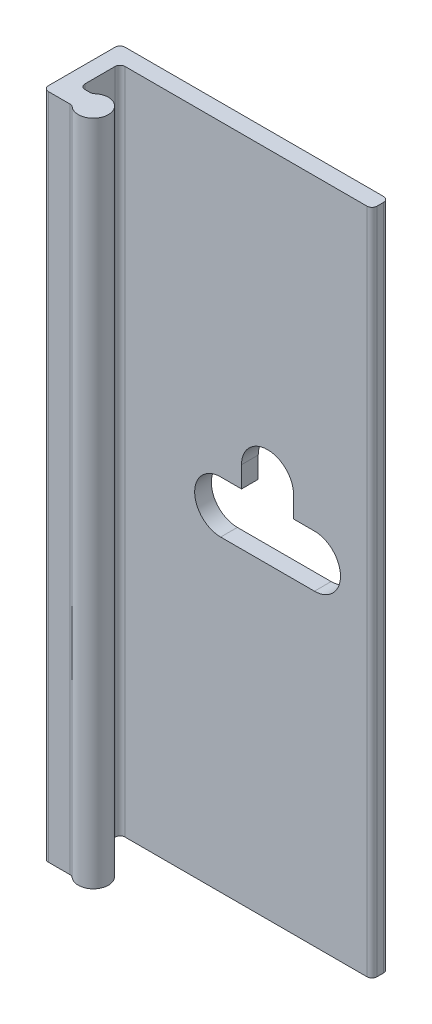
SolidWorks part; units mm, degrees
ref_plane "Front Plane" through (0, 0, 0) normal (0, 0, 1) x (1, 0, 0)
ref_plane "Top Plane" through (0, 0, 0) normal (0, 1, 0) x (1, 0, 0)
ref_plane "Right Plane" through (0, 0, 0) normal (1, 0, 0) x (0, 0, -1)
sketch "Sketch2" plane through (0, 0, 0) normal (0, 1, 0) x (1, 0, 0)
  line L0 (0, 7.209) -> (0, -15.6826) construction
  line L16 (-5.969, 0) -> (19.431, 0)
  line L18 (19.812, -0.381) -> (19.812, -0.889)
  line L19 (19.431, -1.27) -> (1.016, -1.27)
  line L20 (0.635, -1.651) -> (0.635, -3.937)
  line L52 (-0.635, -1.651) -> (-0.635, -3.937)
  line L53 (-8.0148, -5.08) -> (8.0148, -5.08) construction
  line L54 (-1.405, -4.318) -> (-1.016, -4.318)
  line L55 (-1.405, -5.842) -> (1.405, -5.842)
  line L56 (1.016, -4.318) -> (1.405, -4.318)
  line L57 (-1.016, -1.27) -> (-5.969, -1.27)
  line L58 (-6.35, -0.889) -> (-6.35, -0.381)
  arc A11 (19.431, 0) -> (19.812, -0.381) centre (19.431, -0.381) cw
  arc A12 (19.812, -0.889) -> (19.431, -1.27) centre (19.431, -0.889) cw
  arc A19 (1.016, -1.27) -> (0.635, -1.651) centre (1.016, -1.651) ccw
  arc A20 (-1.657, -4.2227) -> (-1.657, -5.9373) centre (-2.413, -5.08) ccw
  arc A21 (1.657, -5.9373) -> (1.657, -4.2227) centre (2.413, -5.08) ccw
  arc A22 (0.635, -3.937) -> (1.016, -4.318) centre (1.016, -3.937) ccw
  arc A23 (-0.635, -3.937) -> (-1.016, -4.318) centre (-1.016, -3.937) cw
  arc A24 (1.405, -5.842) -> (1.657, -5.9373) centre (1.405, -6.223) cw
  arc A25 (1.657, -4.2227) -> (1.405, -4.318) centre (1.405, -3.937) cw
  arc A26 (-1.405, -5.842) -> (-1.657, -5.9373) centre (-1.405, -6.223) ccw
  arc A27 (-1.405, -4.318) -> (-1.657, -4.2227) centre (-1.405, -3.937) cw
  arc A28 (-6.35, -0.381) -> (-5.969, 0) centre (-5.969, -0.381) cw
  arc A29 (-5.969, -1.27) -> (-6.35, -0.889) centre (-5.969, -0.889) cw
  arc A30 (-1.016, -1.27) -> (-0.635, -1.651) centre (-1.016, -1.651) cw
  point P7 (0, -5.08)
  point P16 (19.812, 0)
  point P19 (19.812, -1.27)
  point P22 (0.635, -1.27)
  point P30 (0.635, -4.318)
  point P36 (1.5611, -5.842)
  point P39 (1.5611, -4.318)
  point P42 (-1.5611, -5.842)
  point P45 (-1.5611, -4.318)
  dimension "D7" = 0.381
  dimension "D6" = 2.286
  dimension "D10" = 1.524
  dimension "D11" = 19.812
  dimension "D12" = 6.35
  dimension "D2" = 1.27
  dimension "D3" = 1.27
  dimension "D4" = 0.635
  dimension "D5" = 5.08
  dimension "D8" = 2.413
  dimension "D9" = 2.413
extrude "Boss-Extrude1" add sketch "Sketch2" along normal blind 50.8
sketch "Sketch4" plane through (0, 0, 0) normal (0, -1, 0) x (1, 0, 0)
  line L0 (19.431, 0) -> (-5.969, 0) construction
  line L1 (-0.635, 0) -> (-6.35, 0)
  line L2 (-0.635, 0) -> (-0.635, 6.223)
  line L3 (-0.635, 6.223) -> (-6.35, 6.223)
  line L4 (-6.35, 0) -> (-6.35, 6.223)
  line L5 (-0.635, 1.651) -> (-0.635, 3.937) construction
  line L6 (-6.35, 0.381) -> (-6.35, 0.889) construction
  arc A0 (-1.657, 5.9373) -> (-1.657, 4.2227) centre (-2.413, 5.08) ccw construction
extrude "Cut-Extrude2" cut sketch "Sketch4" against normal through all
fillet "Fillet1" radius 0.381 2 edges at (-0.635, 25.4, 5.842) (-0.635, 25.4, 0)
sketch "Sketch3" plane through (0, 0, 1.27) normal (0, 0, 1) x (1, 0, 0)
  line L0 (8.2931, 25.4) -> (15.4305, 25.4) construction
  line L1 (8.2931, 27.3812) -> (9.8806, 27.3812)
  line L2 (8.2931, 23.4188) -> (15.4305, 23.4188)
  line L3 (19.812, 50.8) -> (19.812, 0) construction
  line L4 (13.843, 28.9814) -> (13.843, 27.3812)
  line L5 (9.8806, 28.9814) -> (9.8806, 27.3812)
  line L6 (13.843, 27.3812) -> (15.4305, 27.3812)
  line L7 (1.016, 0) -> (19.431, 0) construction
  arc A0 (8.2931, 27.3812) -> (8.2931, 23.4188) centre (8.2931, 25.4) ccw
  arc A1 (15.4305, 23.4188) -> (15.4305, 27.3812) centre (15.4305, 25.4) ccw
  arc A2 (13.843, 28.9814) -> (9.8806, 28.9814) centre (11.8618, 28.9814) ccw
  point P2 (11.8618, 25.4)
  dimension "D2" = 1.9812
  dimension "D3" = 3.5814
  dimension "D1" = 7.1374
  dimension "D4" = 7.9502
  dimension "D5" = 25.4
extrude "Cut-Extrude1" cut sketch "Sketch3" against normal through all
pattern_linear "LPattern1" [suppressed] count 2 spacing 203.2
